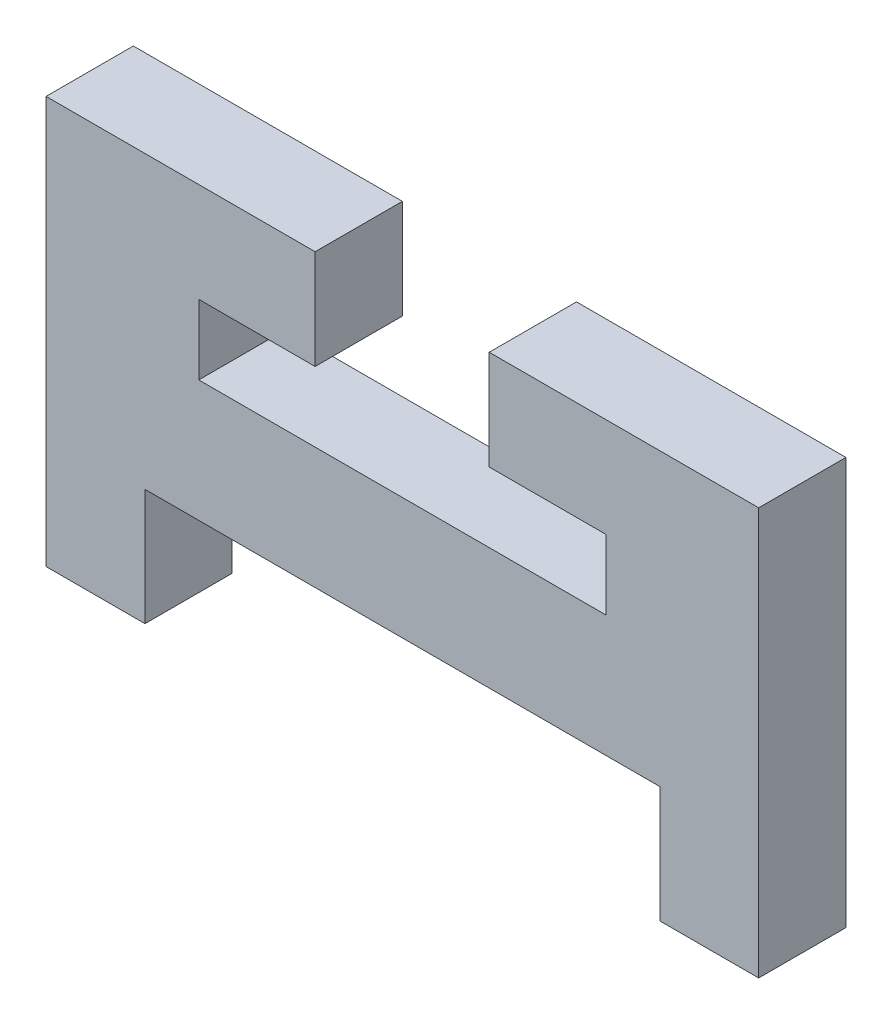
SolidWorks part; units mm, degrees
ref_plane "Alzado" through (0, 0, 0) normal (0, 0, 1) x (1, 0, 0)
ref_plane "Planta" through (0, 0, 0) normal (0, 1, 0) x (1, 0, 0)
ref_plane "Vista lateral" through (0, 0, 0) normal (1, 0, 0) x (0, 0, -1)
sketch "Model" plane through (0, 0, 0) normal (0, 0, 1) x (1, 0, 0)
  line L0 (46.92, 30.0827) -> (39.42, 30.0827)
  line L1 (39.42, 30.0827) -> (39.42, 32.4827)
  line L2 (39.42, 32.4827) -> (43.42, 32.4827)
  line L3 (43.42, 32.4827) -> (43.42, 35.9)
  line L4 (43.42, 35.9) -> (34.17, 35.9)
  line L5 (34.17, 35.9) -> (34.17, 21.9)
  line L6 (34.17, 21.9) -> (37.57, 21.9)
  line L7 (37.57, 21.9) -> (37.57, 25.9)
  line L8 (37.57, 25.9) -> (55.27, 25.9)
  line L9 (55.27, 25.9) -> (55.27, 21.9)
  line L10 (55.27, 21.9) -> (58.67, 21.9)
  line L11 (58.67, 21.9) -> (58.67, 35.9)
  line L12 (58.67, 35.9) -> (49.4064, 35.9)
  line L13 (49.4064, 35.9) -> (49.4064, 32.4827)
  line L14 (49.4064, 32.4827) -> (53.42, 32.4827)
  line L15 (53.42, 32.4827) -> (53.42, 30.0827)
  line L16 (53.42, 30.0827) -> (46.92, 30.0827)
extrude "Saliente-Extruir1" add sketch "Model" along normal blind 3
